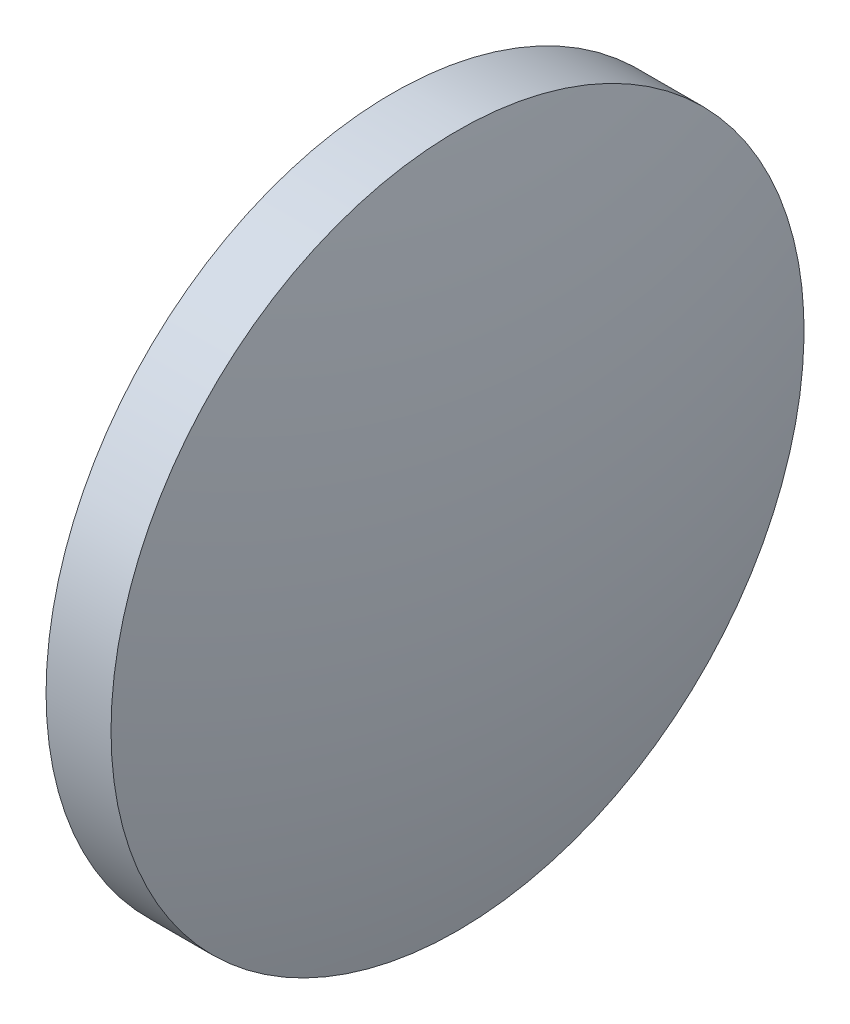
SolidWorks part; units mm, degrees
ref_plane "前视基准面" through (0, 0, 0) normal (0, 0, 1) x (1, 0, 0)
ref_plane "上视基准面" through (0, 0, 0) normal (0, 1, 0) x (1, 0, 0)
ref_plane "右视基准面" through (0, 0, 0) normal (1, 0, 0) x (0, 0, -1)
sketch "草图2" plane through (0, 0, 0) normal (0, 0, 1) x (1, 0, 0)
  line L0 (522.2375, 67.7771) -> (530.5048, 67.7771) construction
  line L1 (524.1603, 67.7771) -> (524.1603, 75.7771)
  line L2 (526.6603, 67.7771) -> (524.1603, 67.7771)
  line L5 (524.1603, 75.7771) -> (525.6603, 75.7771)
  arc A0 (526.6603, 67.7771) -> (525.6603, 75.7771) centre (494.1603, 67.7771) ccw
revolve "旋转2" add sketch "草图2" angle 360 about L0
